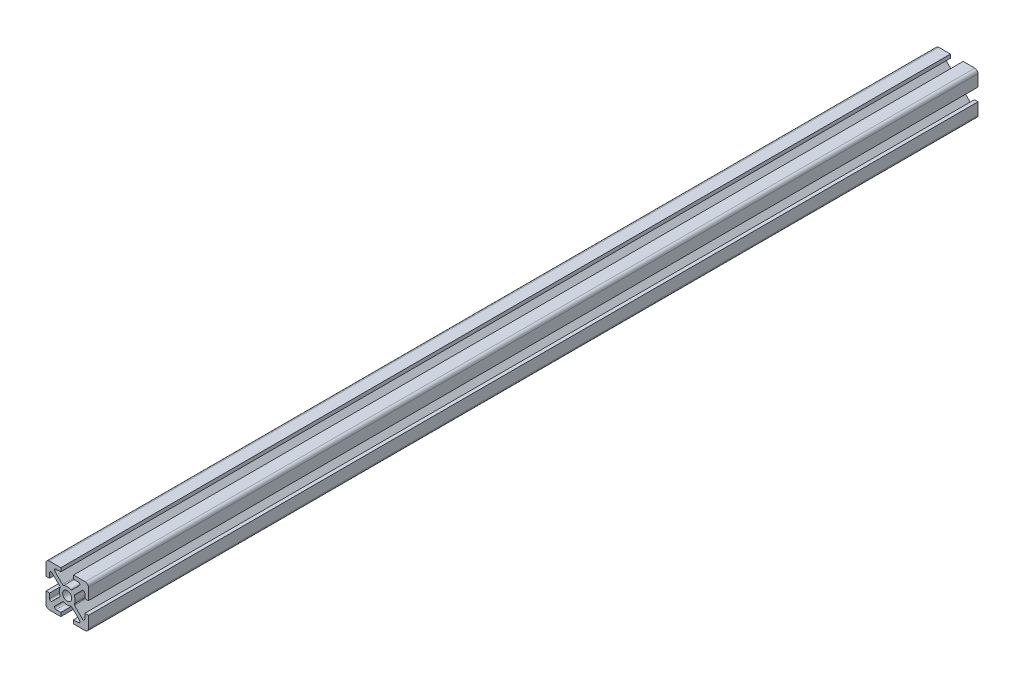
SolidWorks part; units mm, degrees
material "6063-T5"
ref_plane "Face" through (0, 0, 0) normal (0, 0, 1) x (1, 0, 0)
ref_plane "Dessus" through (0, 0, 0) normal (0, 1, 0) x (1, 0, 0)
ref_plane "Droite" through (0, 0, 0) normal (1, 0, 0) x (0, 0, -1)
sketch "Esquisse1" plane through (0, 0, 0) normal (0, 0, 1) x (1, 0, 0)
  line L0 (-3, 10) -> (-8.5, 10)
  line L2 (-3, -10) -> (-3, -8.3)
  line L3 (-3, -8.3) -> (-5.2994, -8.3)
  line L4 (-5.7944, -7.105) -> (-2.1755, -3.4861)
  line L6 (2.1755, -3.4861) -> (5.7944, -7.105)
  line L7 (5.2994, -8.3) -> (3, -8.3)
  line L8 (3, -8.3) -> (3, -10)
  line L11 (3, -10) -> (8.5, -10)
  line L12 (10, -8.5) -> (10, -3)
  line L15 (10, -3) -> (8.3, -3)
  line L16 (8.3, -3) -> (8.3, -5.2994)
  line L17 (7.105, -5.7944) -> (3.4861, -2.1755)
  line L20 (3.4861, 2.1755) -> (7.105, 5.7944)
  line L21 (8.3, 5.2994) -> (8.3, 3)
  line L22 (8.3, 3) -> (10, 3)
  line L25 (10, 3) -> (10, 8.5)
  line L26 (8.5, 10) -> (3.5, 10)
  line L29 (3, 10) -> (3, 8.3)
  line L30 (3, 8.3) -> (5.2994, 8.3)
  line L31 (5.7944, 7.105) -> (2.1755, 3.4861)
  line L34 (-2.1755, 3.4861) -> (-5.7944, 7.105)
  line L35 (-5.2994, 8.3) -> (-3, 8.3)
  line L36 (-3, 8.3) -> (-3, 10)
  line L39 (3.5, 10) -> (3, 10)
  line L40 (-10, 8.5) -> (-10, 3)
  line L43 (-10, 3) -> (-8.3, 3)
  line L44 (-8.3, 3) -> (-8.3, 5.2994)
  line L45 (-7.105, 5.7944) -> (-3.4861, 2.1755)
  line L48 (-3.4861, -2.1755) -> (-7.105, -5.7944)
  line L49 (-8.3, -5.2994) -> (-8.3, -3)
  line L50 (-8.3, -3) -> (-10, -3)
  line L53 (-10, -3) -> (-10, -8.5)
  line L54 (-8.5, -10) -> (-3, -10)
  line L55 (13.1941, 0) -> (-16.3684, 0) construction
  line L56 (0, 3.75) -> (0, -15.1011) construction
  line L58 (5.7944, 5.7944) -> (-5.2994, -5.2994) construction
  line L59 (5.7944, -5.7944) -> (-5.4107, 5.4107) construction
  circle A0 centre (0, 0) radius 2.15
  arc A1 (-5.2994, -8.3) -> (-5.7944, -7.105) centre (-5.2994, -7.6) cw
  arc A2 (-2.1755, -3.4861) -> (-1.6076, -3.388) centre (-1.8219, -3.8397) cw
  arc A3 (-1.6076, -3.388) -> (1.6076, -3.388) centre (0, 0) ccw
  arc A5 (1.6076, -3.388) -> (2.1755, -3.4861) centre (1.8219, -3.8397) cw
  arc A6 (5.7944, -7.105) -> (5.2994, -8.3) centre (5.2994, -7.6) cw
  arc A7 (8.5, -10) -> (10, -8.5) centre (8.5, -8.5) ccw
  arc A8 (8.3, -5.2994) -> (7.105, -5.7944) centre (7.6, -5.2994) cw
  arc A9 (3.4861, -2.1755) -> (3.388, -1.6076) centre (3.8397, -1.8219) cw
  arc A10 (3.388, -1.6076) -> (3.75, 0) centre (0, 0) ccw
  arc A11 (3.75, 0) -> (3.388, 1.6076) centre (0, 0) ccw
  arc A12 (3.388, 1.6076) -> (3.4861, 2.1755) centre (3.8397, 1.8219) cw
  arc A13 (7.105, 5.7944) -> (8.3, 5.2994) centre (7.6, 5.2994) cw
  arc A14 (10, 8.5) -> (8.5, 10) centre (8.5, 8.5) ccw
  arc A15 (5.2994, 8.3) -> (5.7944, 7.105) centre (5.2994, 7.6) cw
  arc A16 (2.1755, 3.4861) -> (1.6076, 3.388) centre (1.8219, 3.8397) cw
  arc A17 (1.6076, 3.388) -> (-1.6076, 3.388) centre (0, 0) ccw
  arc A19 (-1.6076, 3.388) -> (-2.1755, 3.4861) centre (-1.8219, 3.8397) cw
  arc A20 (-5.7944, 7.105) -> (-5.2994, 8.3) centre (-5.2994, 7.6) cw
  arc A21 (-8.5, 10) -> (-10, 8.5) centre (-8.5, 8.5) ccw
  arc A22 (-8.3, 5.2994) -> (-7.105, 5.7944) centre (-7.6, 5.2994) cw
  arc A23 (-3.4861, 2.1755) -> (-3.388, 1.6076) centre (-3.8397, 1.8219) cw
  arc A24 (-3.388, 1.6076) -> (-3.388, -1.6076) centre (0, 0) ccw
  arc A26 (-3.388, -1.6076) -> (-3.4861, -2.1755) centre (-3.8397, -1.8219) cw
  arc A27 (-7.105, -5.7944) -> (-8.3, -5.2994) centre (-7.6, -5.2994) cw
  arc A28 (-10, -8.5) -> (-8.5, -10) centre (-8.5, -8.5) ccw
  dimension "D3" = 4.3
  dimension "D4" = 1.5
  dimension "D15" = 0.7
  dimension "D19" = 3.75
  dimension "D20" = 0.5
  dimension "D1" = 20
  dimension "D2" = 20
  dimension "D10" = 10
  dimension "D11" = 10
  dimension "D12" = 3
  dimension "D13" = 3
  dimension "D16" = 1.7
  dimension "D17" = 5.2994
  dimension "D18" = 45
  dimension "D22" = 45
  dimension "D23" = 6
  dimension "D24" = 45
  dimension "D25" = 5.2994
  dimension "D26" = 45
extrude "Boss.-Extru.1" add sketch "Esquisse1" along normal blind 420
